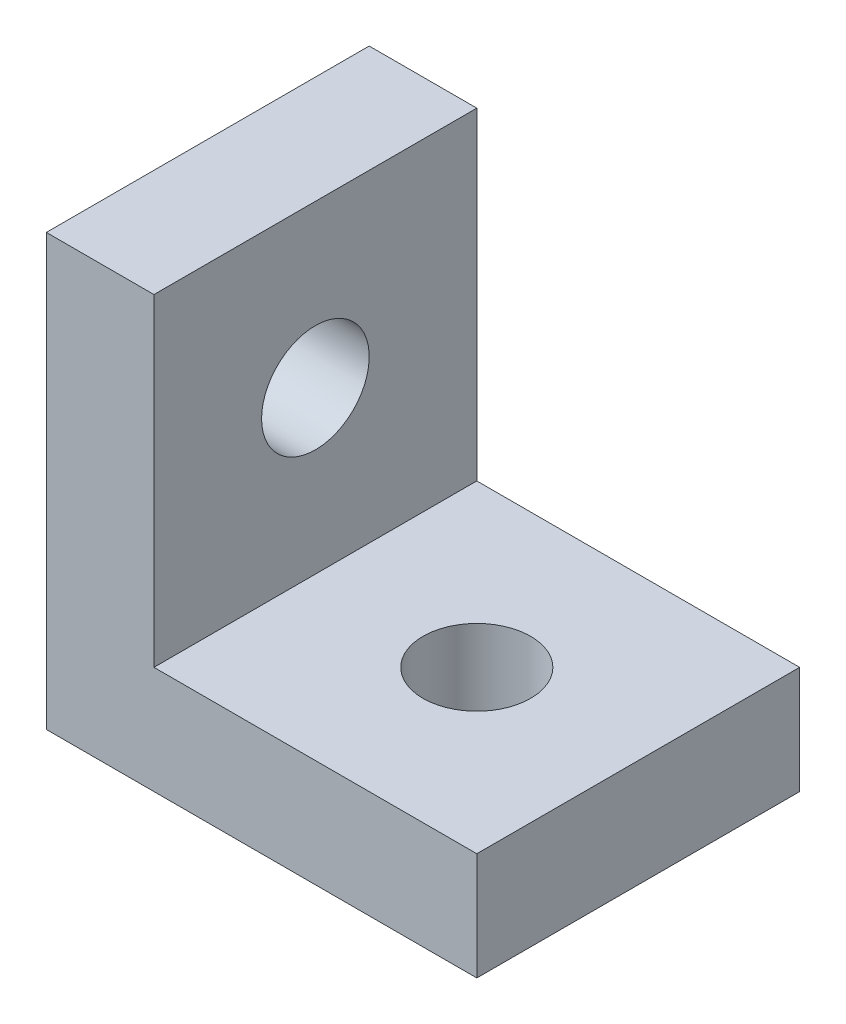
SolidWorks part; units mm, degrees
ref_plane "Front Plane" through (0, 0, 0) normal (0, 0, 1) x (1, 0, 0)
ref_plane "Top Plane" through (0, 0, 0) normal (0, 1, 0) x (1, 0, 0)
ref_plane "Right Plane" through (0, 0, 0) normal (1, 0, 0) x (0, 0, -1)
sketch "Sketch1" plane through (0, 0, 0) normal (0, 0, 1) x (1, 0, 0)
  line L0 (0, 0) -> (10, 10)
  line L1 (10, 10) -> (40, 10)
  line L2 (40, 10) -> (40, 0)
  line L3 (40, 0) -> (0, 0)
  dimension "D1" = 40
  dimension "D2" = 10
  dimension "D3" = 45
extrude "Boss-Extrude1" add sketch "Sketch1" along normal blind 30
sketch "Sketch2" plane through (0, 10, 0) normal (0, 1, 0) x (1, 0, 0)
  line L0 (40, -30) -> (40, 0) construction
  line L1 (40, -30) -> (10, -30) construction
  circle A0 centre (25, -15) radius 5
  dimension "D1" = 10
  dimension "D2" = 15
  dimension "D3" = 15
extrude "Cut-Extrude1" cut sketch "Sketch2" against normal blind 30
mirror "Mirror1" about plane through (0, 0, 30) normal (0.7071, -0.7071, 0) of bodies 102
